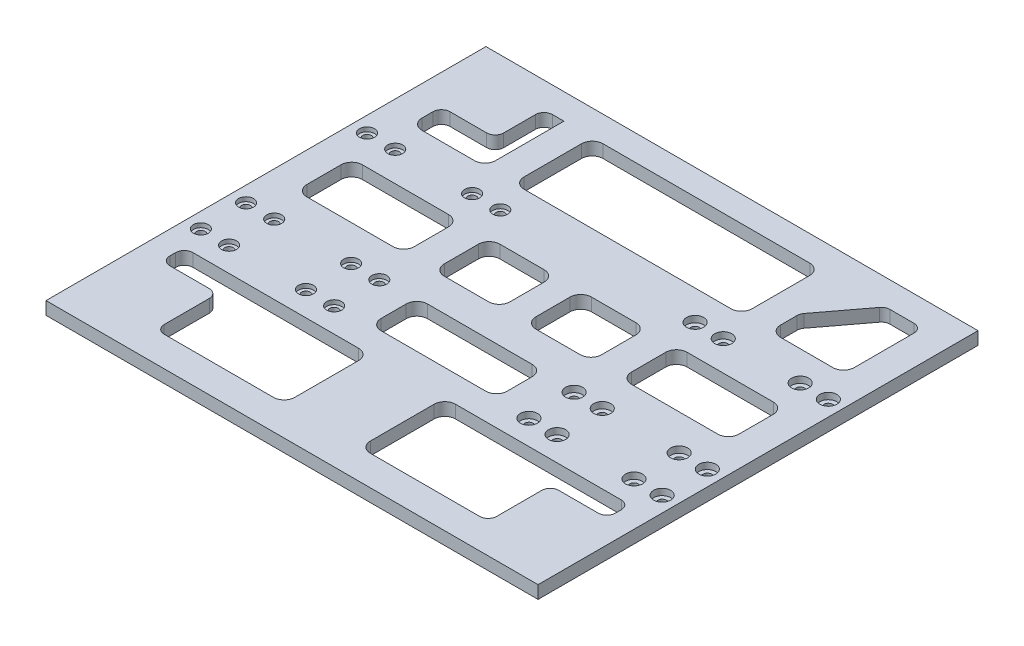
SolidWorks part; units mm, degrees
material "Custom Plastic"
ref_plane "Front Plane" through (0, 0, 0) normal (0, 0, 1) x (1, 0, 0)
ref_plane "Top Plane" through (0, 0, 0) normal (0, 1, 0) x (1, 0, 0)
ref_plane "Right Plane" through (0, 0, 0) normal (1, 0, 0) x (0, 0, -1)
sketch "Sketch1" plane through (0, 0, 0) normal (0, 1, 0) x (1, 0, 0)
  line L1 (-57.5, -51.5) -> (57.5, -51.5)
  line L2 (-57.5, -51.5) -> (-57.5, 51.5)
  line L3 (-57.5, 51.5) -> (57.5, 51.5)
  line L4 (57.5, -51.5) -> (57.5, 51.5)
  line L5 (-57.5, -51.5) -> (57.5, 51.5) construction
  line L6 (-57.5, 51.5) -> (57.5, -51.5) construction
  point P0 (0, 0)
  dimension "D1" = 115
  dimension "D2" = 103
extrude "Boss-Extrude1" add sketch "Sketch1" along normal blind 3
sketch "Sketch2" plane through (0, 0, 0) normal (0, -1, 0) x (1, 0, 0)
  line L0 (-57.5, 51.5) -> (57.5, 51.5) construction
  line L2 (0, 51.5) -> (0, -51.5) construction
  line L3 (57.5, -51.5) -> (-57.5, -51.5) construction
  line L4 (-47.4, 51.5) -> (-47.4, -51.5) construction
  line L5 (-38.4, -51.5) -> (-38.4, 45.883) construction
  line L6 (-29.4, -51.5) -> (-29.4, 45.883) construction
  line L7 (-22.8, 18.84) -> (-22.8, -20.06) construction
  line L8 (-54, 18.84) -> (-54, -20.06) construction
  circle A0 centre (-54, -20.06) radius 1
  circle A1 centre (-54, 8.27) radius 1
  circle A2 centre (-54, 18.84) radius 1
  circle A3 centre (54, -20.06) radius 1
  circle A4 centre (54, 8.27) radius 1
  circle A5 centre (54, 18.84) radius 1
  circle A6 centre (-47.4, 18.84) radius 1
  circle A7 centre (-47.4, -20.06) radius 1
  circle A8 centre (-47.4, 8.27) radius 1
  circle A9 centre (47.4, -20.06) radius 1
  circle A10 centre (47.4, 8.27) radius 1
  circle A11 centre (47.4, 18.84) radius 1
  circle A12 centre (-29.4, 18.84) radius 1
  circle A13 centre (-22.8, 18.84) radius 1
  circle A14 centre (-22.8, 8.27) radius 1
  circle A15 centre (-29.4, 8.27) radius 1
  circle A16 centre (-22.8, -20.06) radius 1
  circle A17 centre (-29.4, -20.06) radius 1
  circle A18 centre (22.8, 18.84) radius 1
  circle A19 centre (29.4, 18.84) radius 1
  circle A20 centre (29.4, 8.27) radius 1
  circle A21 centre (22.8, 8.27) radius 1
  circle A22 centre (29.4, -20.06) radius 1
  circle A23 centre (22.8, -20.06) radius 1
  point P50 (0, 0)
  point P51 (0, 0)
  dimension "D7" = 2
  dimension "D8" = 2
  dimension "D9" = 2
  dimension "D12" = 2
  dimension "D14" = 2
  dimension "D15" = 43.23
  dimension "D16" = 2
  dimension "D1" = 32.66
  dimension "D2" = 43.23
  dimension "D3" = 71.56
  dimension "D4" = 6.6
  dimension "D5" = 22.8
  dimension "D11" = 32.66
  dimension "D13" = 71.56
  dimension "D17" = 18
  dimension "D18" = 9
extrude "Cut-Extrude1" cut sketch "Sketch2" against normal blind 10
sketch "Sketch3" plane through (-57.5, 0, 0) normal (-1, 0, 0) x (0, 0, 1)
  line L8 (-51.5, 0) -> (51.5, 0)
  line L9 (51.5, 0) -> (51.5, 3)
  line L10 (51.5, 3) -> (-51.5, 3)
  line L11 (-51.5, 3) -> (-51.5, 0)
  line L12 (-51.5, 0) -> (51.5, 0)
  line L13 (51.5, 0) -> (51.5, 3)
  line L14 (51.5, 3) -> (-51.5, 3)
  line L15 (-51.5, 3) -> (-51.5, 0)
  dimension "D1" = 0
extrude "Boss-Extrude2" add sketch "Sketch3" along normal blind 0.1
sketch "Sketch4" plane through (57.5, 0, 0) normal (1, 0, 0) x (0, 0, -1)
  line L4 (-51.5, 0) -> (51.5, 0)
  line L5 (51.5, 0) -> (51.5, 3)
  line L6 (51.5, 3) -> (-51.5, 3)
  line L7 (-51.5, 3) -> (-51.5, 0)
  line L8 (-51.5, 0) -> (51.5, 0)
  line L9 (51.5, 0) -> (51.5, 3)
  line L10 (51.5, 3) -> (-51.5, 3)
  line L11 (-51.5, 3) -> (-51.5, 0)
  dimension "D1" = 0
extrude "Boss-Extrude3" add sketch "Sketch4" along normal blind 0.1
sketch "Sketch6" plane through (0, 3, 0) normal (0, 1, 0) x (1, 0, 0)
  line L0 (-40.0136, 34.0806) -> (-48.6, 34.0806)
  line L1 (-50.6, 32.0806) -> (-50.6, 29.5256)
  line L2 (-48.1, 27.0256) -> (-35.8465, 27.0256)
  line L3 (-33.3465, 29.5256) -> (-33.3465, 34.0806)
  line L4 (-38.0136, 36.0806) -> (-38.0136, 43.5)
  line L6 (0, 64.7841) -> (0, -71.4614) construction
  line L7 (-24.2114, 45.5) -> (24.2114, 45.5)
  line L8 (-26.7114, 43) -> (-26.7114, 29.5256)
  line L9 (-24.2114, 27.0256) -> (24.2114, 27.0256)
  line L10 (26.7114, 43) -> (26.7114, 29.5256)
  line L11 (-52.1542, -26.5754) -> (-52.1542, -27.9538)
  line L12 (-48.1, 0.0564) -> (-27.9271, 0.0564)
  line L13 (-50.6, 2.5564) -> (-50.6, 10.569)
  line L14 (-48.1, 13.069) -> (-27.9271, 13.069)
  line L15 (-25.4271, 2.5564) -> (-25.4271, 10.569)
  line L16 (-50.6, 0.0564) -> (-25.4271, 13.069) construction
  line L17 (-50.6, 13.069) -> (-25.4271, 0.0564) construction
  line L18 (-15.9179, 0.0564) -> (-5.5337, 0.0564)
  line L19 (-18.4179, 2.5564) -> (-18.4179, 10.569)
  line L20 (-15.9179, 13.069) -> (-5.5337, 13.069)
  line L21 (-3.0337, 2.5564) -> (-3.0337, 10.569)
  line L22 (-18.4179, 0.0564) -> (-3.0337, 13.069) construction
  line L23 (-18.4179, 13.069) -> (-3.0337, 0.0564) construction
  line L24 (-36.9158, -44.5) -> (-11.3488, -44.5)
  line L25 (-50.1542, -29.9538) -> (-40.9158, -29.9538)
  line L26 (-50.1542, -24.5754) -> (-11.3488, -24.5754)
  line L27 (-8.8488, -42) -> (-8.8488, -27.0754)
  line L28 (-38.9158, -31.9538) -> (-38.9158, -42.5)
  line L29 (8.8488, -42) -> (8.8488, -27.0754)
  line L30 (-57.6, -51.5) -> (-57.6, 51.5) construction
  line L31 (-36.0136, 45.5) -> (-33.3465, 45.5)
  line L32 (-57.6, -51.5) -> (57.6, -51.5) construction
  line L33 (50.1542, -24.5754) -> (11.3488, -24.5754)
  line L34 (-12.2501, -18.3965) -> (12.2501, -18.3965)
  line L35 (-14.7501, -15.8965) -> (-14.7501, -10.0236)
  line L36 (-12.2501, -7.5236) -> (12.2501, -7.5236)
  line L37 (14.7501, -15.8965) -> (14.7501, -10.0236)
  line L38 (-14.7501, -18.3965) -> (14.7501, -7.5236) construction
  line L39 (-14.7501, -7.5236) -> (14.7501, -18.3965) construction
  line L40 (52.1542, -26.5754) -> (52.1542, -27.9538)
  line L41 (50.1542, -29.9538) -> (40.9158, -29.9538)
  line L42 (38.9158, -31.9538) -> (38.9158, -42.5)
  line L43 (36.9158, -44.5) -> (11.3488, -44.5)
  line L44 (3.0337, 2.5564) -> (3.0337, 10.569)
  line L45 (15.9179, 13.069) -> (5.5337, 13.069)
  line L46 (18.4179, 2.5564) -> (18.4179, 10.569)
  line L47 (15.9179, 0.0564) -> (5.5337, 0.0564)
  line L48 (48.1, 0.0564) -> (27.9271, 0.0564)
  line L49 (50.6, 2.5564) -> (50.6, 10.569)
  line L50 (48.1, 13.069) -> (27.9271, 13.069)
  line L51 (25.4271, 2.5564) -> (25.4271, 10.569)
  line L52 (48.1, 27.0256) -> (35.8465, 27.0256)
  line L53 (50.6, 34.0806) -> (50.6, 29.5256)
  line L54 (50.6, 34.0806) -> (50.6, 43.5)
  line L55 (48.6, 45.5) -> (42.9689, 45.5)
  line L56 (33.3465, 29.5256) -> (33.3465, 33.4101)
  line L57 (-33.3465, 45.5) -> (-33.3465, 34.0806)
  line L58 (-33.3465, 34.0806) -> (-33.3808, 34.0834)
  line L59 (41.3731, 44.7056) -> (33.7507, 34.6157)
  arc A0 (-50.6, 32.0806) -> (-48.6, 34.0806) centre (-48.6, 32.0806) cw
  arc A1 (-38.0136, 43.5) -> (-36.0136, 45.5) centre (-36.0136, 43.5) cw
  arc A2 (-50.1542, -24.5754) -> (-52.1542, -26.5754) centre (-50.1542, -26.5754) ccw
  arc A3 (-52.1542, -27.9538) -> (-50.1542, -29.9538) centre (-50.1542, -27.9538) ccw
  arc A4 (-40.9158, -29.9538) -> (-38.9158, -31.9538) centre (-40.9158, -31.9538) cw
  arc A5 (-11.3488, -44.5) -> (-8.8488, -42) centre (-11.3488, -42) ccw
  arc A6 (-11.3488, -24.5754) -> (-8.8488, -27.0754) centre (-11.3488, -27.0754) cw
  arc A7 (12.2501, -7.5236) -> (14.7501, -10.0236) centre (12.2501, -10.0236) cw
  arc A8 (12.2501, -18.3965) -> (14.7501, -15.8965) centre (12.2501, -15.8965) ccw
  arc A9 (-12.2501, -18.3965) -> (-14.7501, -15.8965) centre (-12.2501, -15.8965) cw
  arc A10 (-14.7501, -10.0236) -> (-12.2501, -7.5236) centre (-12.2501, -10.0236) cw
  arc A11 (-27.9271, 13.069) -> (-25.4271, 10.569) centre (-27.9271, 10.569) cw
  arc A12 (-27.9271, 0.0564) -> (-25.4271, 2.5564) centre (-27.9271, 2.5564) ccw
  arc A13 (-48.1, 0.0564) -> (-50.6, 2.5564) centre (-48.1, 2.5564) cw
  arc A14 (-50.6, 10.569) -> (-48.1, 13.069) centre (-48.1, 10.569) cw
  arc A15 (24.2114, 27.0256) -> (26.7114, 29.5256) centre (24.2114, 29.5256) ccw
  arc A16 (24.2114, 45.5) -> (26.7114, 43) centre (24.2114, 43) cw
  arc A17 (-5.5337, 13.069) -> (-3.0337, 10.569) centre (-5.5337, 10.569) cw
  arc A18 (-5.5337, 0.0564) -> (-3.0337, 2.5564) centre (-5.5337, 2.5564) ccw
  arc A19 (-15.9179, 0.0564) -> (-18.4179, 2.5564) centre (-15.9179, 2.5564) cw
  arc A20 (-18.4179, 10.569) -> (-15.9179, 13.069) centre (-15.9179, 10.569) cw
  arc A21 (-24.2114, 45.5) -> (-26.7114, 43) centre (-24.2114, 43) ccw
  arc A22 (-26.7114, 29.5256) -> (-24.2114, 27.0256) centre (-24.2114, 29.5256) ccw
  arc A23 (-35.8465, 27.0256) -> (-33.3465, 29.5256) centre (-35.8465, 29.5256) ccw
  arc A24 (-38.0136, 36.0806) -> (-40.0136, 34.0806) centre (-40.0136, 36.0806) cw
  arc A25 (-50.6, 29.5256) -> (-48.1, 27.0256) centre (-48.1, 29.5256) ccw
  arc A26 (-36.9158, -44.5) -> (-38.9158, -42.5) centre (-36.9158, -42.5) cw
  arc A27 (11.3488, -24.5754) -> (8.8488, -27.0754) centre (11.3488, -27.0754) ccw
  arc A28 (50.1542, -24.5754) -> (52.1542, -26.5754) centre (50.1542, -26.5754) cw
  arc A29 (52.1542, -27.9538) -> (50.1542, -29.9538) centre (50.1542, -27.9538) cw
  arc A30 (40.9158, -29.9538) -> (38.9158, -31.9538) centre (40.9158, -31.9538) ccw
  arc A31 (5.5337, 0.0564) -> (3.0337, 2.5564) centre (5.5337, 2.5564) cw
  arc A32 (5.5337, 13.069) -> (3.0337, 10.569) centre (5.5337, 10.569) ccw
  arc A33 (18.4179, 10.569) -> (15.9179, 13.069) centre (15.9179, 10.569) ccw
  arc A34 (15.9179, 0.0564) -> (18.4179, 2.5564) centre (15.9179, 2.5564) ccw
  arc A35 (27.9271, 13.069) -> (25.4271, 10.569) centre (27.9271, 10.569) ccw
  arc A36 (27.9271, 0.0564) -> (25.4271, 2.5564) centre (27.9271, 2.5564) cw
  arc A37 (48.1, 0.0564) -> (50.6, 2.5564) centre (48.1, 2.5564) ccw
  arc A38 (50.6, 10.569) -> (48.1, 13.069) centre (48.1, 10.569) ccw
  arc A39 (35.8465, 27.0256) -> (33.3465, 29.5256) centre (35.8465, 29.5256) cw
  arc A40 (50.6, 29.5256) -> (48.1, 27.0256) centre (48.1, 29.5256) cw
  arc A41 (33.7507, 34.6157) -> (33.3465, 33.4101) centre (35.3465, 33.4101) ccw
  arc A42 (42.9689, 45.5) -> (41.3731, 44.7056) centre (42.9689, 43.5) ccw
  arc A43 (50.6, 43.5) -> (48.6, 45.5) centre (48.6, 43.5) ccw
  arc A44 (36.9158, -44.5) -> (38.9158, -42.5) centre (36.9158, -42.5) ccw
  arc A45 (11.3488, -44.5) -> (8.8488, -42) centre (11.3488, -42) cw
  point P14 (0, 45.5)
  point P15 (-38.0136, 6.5627)
  point P20 (-10.7258, 6.5627)
  point P26 (-31.1437, -33.7327)
  point P36 (0, -12.9601)
  point P43 (-50.6, 34.0806)
  point P158 (33.3465, 34.0806)
  dimension "D6" = 2
  dimension "D1" = 2
  dimension "D2" = 2
  dimension "D3" = 7
  dimension "D4" = 7
  dimension "D5" = 7
extrude "Cut-Extrude3" cut sketch "Sketch6" against normal blind 10
sketch "Sketch8" plane through (0, 3, 0) normal (0, 1, 0) x (1, 0, 0)
  circle A0 centre (54, -18.84) radius 2
  circle A1 centre (47.4, -18.84) radius 2.0011
  circle A2 centre (54, -8.27) radius 2
  circle A3 centre (47.4, -8.27) radius 2
  circle A4 centre (54, 20.06) radius 2
  circle A5 centre (47.4, 20.06) radius 2
  circle A6 centre (29.4, 20.06) radius 2
  circle A7 centre (22.8, 20.06) radius 2
  circle A8 centre (22.8, -18.84) radius 2
  circle A9 centre (29.4, -18.84) radius 2
  circle A10 centre (29.4, -8.27) radius 2
  circle A11 centre (22.8, -8.27) radius 2
  dimension "D1" = 4
  dimension "D2" = 4.0022
  dimension "D3" = 4
  dimension "D4" = 4
  dimension "D5" = 4
  dimension "D6" = 4
  dimension "D7" = 4
  dimension "D8" = 4
  dimension "D9" = 4
  dimension "D10" = 4
  dimension "D11" = 4
  dimension "D12" = 4
extrude "Cut-Extrude5" cut sketch "Sketch8" against normal blind 1.5
ref_plane "Plane1" through (0, 0, 0) normal (-1, 0, 0) x (0, 0, 1)
sketch "Sketch7" plane through (0, 3, 0) normal (0, 1, 0) x (1, 0, 0)
  line L0 (0, 51.5) -> (0, -52.1311) construction
  line L1 (57.6, 51.5) -> (-57.6, 51.5) construction
  line L2 (-38.4, 51.5) -> (-38.4, -51.5) construction
  line L3 (-57.6, -51.5) -> (57.6, -51.5) construction
  circle A0 centre (-54, 20.06) radius 1.75
  circle A1 centre (-47.4, 20.06) radius 1.75
  circle A2 centre (-54, -8.27) radius 1.75
  circle A3 centre (-47.4, -8.27) radius 1.75
  circle A4 centre (-54, -18.84) radius 1.75
  circle A5 centre (-47.4, -18.84) radius 1.75
  circle A6 centre (-29.4, -18.84) radius 1.75
  circle A7 centre (-22.8, -18.84) radius 1.75
  circle A8 centre (-29.4, -8.27) radius 1.75
  circle A9 centre (-22.8, -8.27) radius 1.75
  circle A10 centre (-22.8, 20.06) radius 1.75
  circle A11 centre (-29.4, 20.06) radius 1.75
  circle A12 centre (22.8, -18.84) radius 1.75
  circle A13 centre (29.4, -18.84) radius 1.75
  circle A14 centre (47.4, -18.84) radius 1.75
  circle A15 centre (54, -18.84) radius 1.75
  circle A16 centre (22.8, -8.27) radius 1.75
  circle A17 centre (29.4, -8.27) radius 1.75
  circle A18 centre (47.4, -8.27) radius 1.75
  circle A19 centre (54, -8.27) radius 1.75
  circle A20 centre (22.8, 20.06) radius 1.75
  circle A21 centre (29.4, 20.06) radius 1.75
  circle A22 centre (47.4, 20.06) radius 1.75
  circle A23 centre (54, 20.06) radius 1.75
  dimension "D1" = 3.5
  dimension "D2" = 3.5
  dimension "D3" = 3.5
  dimension "D4" = 3.5
  dimension "D5" = 3.5
  dimension "D6" = 3.5
  dimension "D7" = 9
extrude "Cut-Extrude4" cut sketch "Sketch7" against normal blind 1
